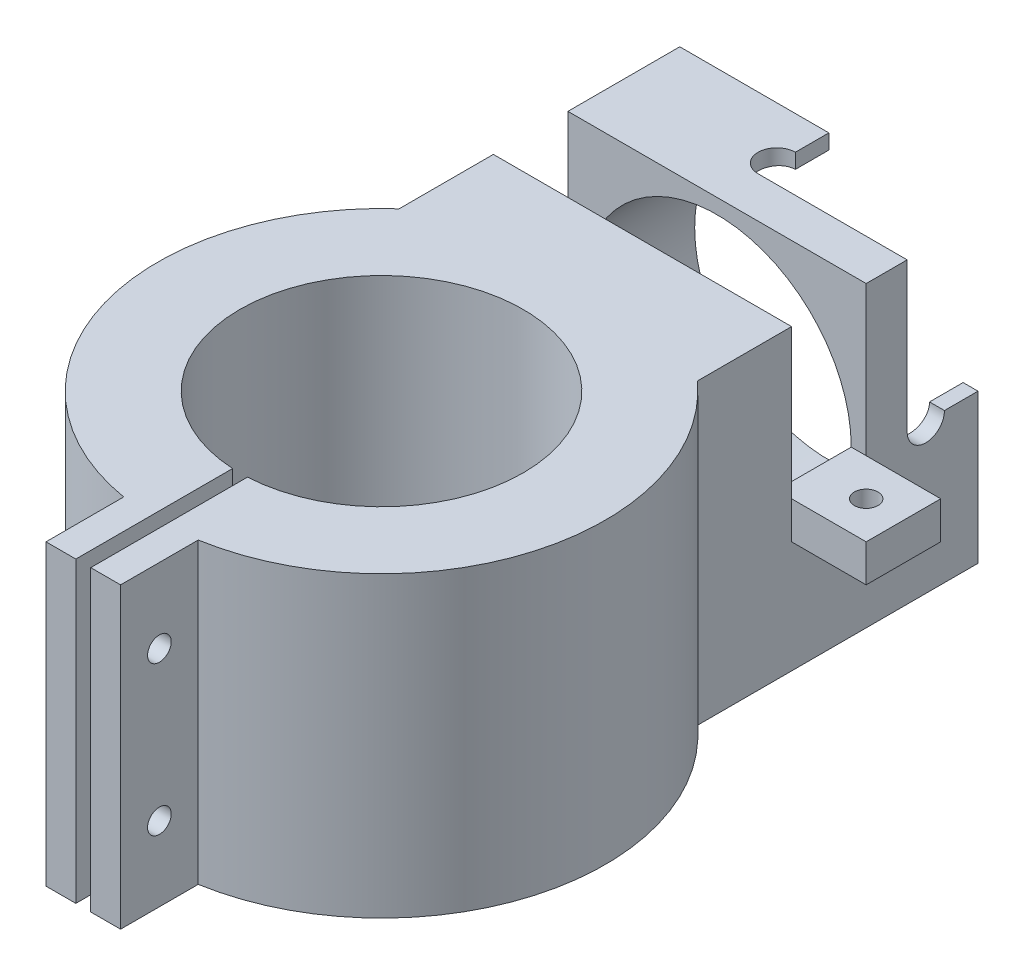
SolidWorks part; units mm, degrees
ref_plane "Front Plane" through (0, 0, 0) normal (0, 0, 1) x (1, 0, 0)
ref_plane "Top Plane" through (0, 0, 0) normal (0, 1, 0) x (1, 0, 0)
ref_plane "Right Plane" through (0, 0, 0) normal (1, 0, 0) x (0, 0, -1)
sketch "Sketch1" plane through (0, 0, 0) normal (0, 1, 0) x (1, 0, 0)
  line L0 (0, 0) -> (0, -40) construction
  line L1 (5, -40) -> (-5, -40)
  line L2 (-5, -40) -> (-5, -29.5804)
  line L3 (5, -40) -> (5, -29.5804)
  line L4 (0, 0) -> (0, 30) construction
  line L5 (-20, 30) -> (20, 30)
  line L6 (-20, 30) -> (-20, 22.3607)
  line L7 (20, 30) -> (20, 22.3607)
  circle A0 centre (0, 0) radius 30 construction
  arc A1 (-5, -29.5804) -> (5, -29.5804) centre (0, 0) cw construction
  circle A2 centre (0, 0) radius 19
  arc A3 (-20, 22.3607) -> (-5, -29.5804) centre (0, 0) ccw
  arc A4 (20, 22.3607) -> (5, -29.5804) centre (0, 0) cw
  point P7 (0, -40)
  point P14 (0, 30)
  dimension "D1" = 60
  dimension "D4" = 38
  dimension "D2" = 40
  dimension "D3" = 10
  dimension "D5" = 40
extrude "Boss-Extrude1" add sketch "Sketch1" along normal blind 40
sketch "Sketch4" plane through (0, 0, -30) normal (0, 0, -1) x (-1, 0, 0)
  line L1 (-20, 40) -> (20, 40)
  line L2 (-20, 40) -> (-20, 0)
  line L3 (-20, 0) -> (20, 0)
  line L4 (20, 40) -> (20, 0)
extrude "Boss-Extrude2" add sketch "Sketch4" along normal blind 30
sketch "Sketch5" plane through (0, 0, -60) normal (0, 0, -1) x (-1, 0, 0)
  line L0 (-20, 40) -> (20, 0) construction
  line L1 (-20, 0) -> (20, 40) construction
  circle A0 centre (0, 20) radius 18
  dimension "D1" = 36
extrude "Cut-Extrude3" cut sketch "Sketch5" against normal blind 30
sketch "Sketch8" plane through (0, 40, 0) normal (0, 1, 0) x (1, 0, 0)
  line L0 (-20, 60) -> (20, 60) construction
  line L1 (-20, 60) -> (-20, 22.3607) construction
  circle A0 centre (0, 53) radius 2.5
  dimension "D1" = 5
  dimension "D2" = 7
  dimension "D3" = 20
extrude "Cut-Extrude5" cut sketch "Sketch8" against normal blind 10
sketch "Sketch7" plane through (0, 0, -60) normal (0, 0, -1) x (-1, 0, 0)
  circle A0 centre (0, 20) radius 20
  circle A1 centre (0, 20) radius 30.1107
  circle A2 centre (0, 20) radius 18 construction
ref_plane "Plane1" through (-10, 10, 0) normal (-0.7071, 0.7071, 0) x (0.7071, 0.7071, 0)
ref_plane "Plane2" [suppressed] through (24.1421, 24.1421, 0) normal (0.7071, 0.7071, 0) x (0, 0, -1)
sketch "Sketch2" plane through (0, 40, 0) normal (0, 1, 0) x (1, 0, 0)
  line L0 (0, -40) -> (0, -19) construction
  line L1 (-5, -40) -> (5, -40) construction
  line L3 (1, -40.0263) -> (-1, -40.0263)
  line L4 (1, -40.0263) -> (1, -18.9737)
  line L5 (1, -18.9737) -> (-1, -18.9737)
  line L6 (-1, -40.0263) -> (-1, -18.9737)
  line L7 (1, -40.0263) -> (-1, -18.9737) construction
  line L8 (1, -18.9737) -> (-1, -40.0263) construction
  circle A0 centre (0, 0) radius 19 construction
  point P7 (0, -29.5)
  dimension "D1" = 2
extrude "Cut-Extrude1" cut sketch "Sketch2" against normal up to surface (40 mm away) up to face at (0, 0, -2.0167)
sketch "Sketch3" plane through (5, 0, 0) normal (1, 0, 0) x (0, 0, -1)
  line L0 (-40, 40) -> (-29.5804, 40) construction
  line L1 (-40, 0) -> (-29.5804, 0) construction
  circle A0 centre (-34.7902, 30) radius 1.5875
  circle A1 centre (-34.7902, 10) radius 1.5875
  dimension "D1" = 3.175
  dimension "D2" = 3.175
  dimension "D3" = 10
  dimension "D4" = 10
extrude "Cut-Extrude2" cut sketch "Sketch3" against normal blind 35
sketch "Sketch9" plane through (0, 40, 0) normal (0, 1, 0) x (1, 0, 0)
  line L0 (-20, 60) -> (-20, 22.3607) construction
  line L1 (-20, 45) -> (20, 45)
  line L2 (-20, 45) -> (-20, 35)
  line L3 (-20, 35) -> (20, 35)
  line L4 (20, 45) -> (20, 35)
  line L5 (20, 22.3607) -> (20, 60) construction
  line L6 (20, 60) -> (-20, 60) construction
  dimension "D1" = 25
  dimension "D2" = 10
extrude "Cut-Extrude6" cut sketch "Sketch9" against normal blind 20
ref_plane "Plane3" through (0, 0, 0) normal (1, 0, 0) x (0, 0, -1)
sketch "Sketch10" plane through (-20, 0, 0) normal (-1, 0, 0) x (0, 0, 1)
  line L0 (-35, 20) -> (-35, 40) construction
  line L1 (-45, 20) -> (-35, 20)
  line L2 (-45, 20) -> (-45, 15)
  line L3 (-45, 15) -> (-35, 15)
  line L4 (-35, 20) -> (-35, 15)
  line L5 (-45, 20) -> (-45, 40) construction
  dimension "D1" = 5
extrude "Boss-Extrude3" add sketch "Sketch10" along normal blind 10
sketch "Sketch11" plane through (0, 20, 0) normal (0, 1, 0) x (1, 0, 0)
  line L0 (-30, 35) -> (-30, 45) construction
  line L1 (-30, 40) -> (-18, 40) construction
  line L2 (-18, 35) -> (-18, 45) construction
  circle A0 centre (-25, 40) radius 1.5875
  dimension "D2" = 3.175
  dimension "D1" = 5
extrude "Cut-Extrude7" cut sketch "Sketch11" against normal up to surface (5 mm away) up to face at (-25, 15, -40)
mirror "Mirror1" about plane through (0, 0, 0) normal (1, 0, 0) of "Cut-Extrude7", "Boss-Extrude3"
ref_plane "Plane4" through (0, 0, -53) normal (0, 0, -1) x (-1, 0, 0)
sketch "Sketch12" plane through (0, 0, -53) normal (0, 0, -1) x (-1, 0, 0)
  line L0 (0, 20) -> (-20, 20)
  line L1 (-20, 40) -> (-20, 0) construction
  line L2 (0, 20) -> (0, 40)
  line L3 (0, 40) -> (-20, 40)
  line L4 (-20, 40) -> (-20, 20)
extrude "Cut-Extrude9" cut sketch "Sketch12" against normal mid plane 5
sketch "Sketch13" plane through (20, 0, 0) normal (1, 0, 0) x (0, 0, -1)
  line L0 (50.5, 20) -> (55.5, 20) construction
  circle A0 centre (53, 20) radius 2.5
extrude "Cut-Extrude10" cut sketch "Sketch13" against normal up to next
sketch "Sketch14" plane through (0, 0, -55.5) normal (0, 0, 1) x (1, 0, 0)
  line L1 (0, 40) -> (20, 40)
  line L2 (0, 40) -> (0, 20)
  line L3 (0, 20) -> (20, 20)
  line L4 (20, 40) -> (20, 20)
extrude "Cut-Extrude11" cut sketch "Sketch14" against normal up to surface (4.5 mm away) up to face at (-18, 20, -60)
